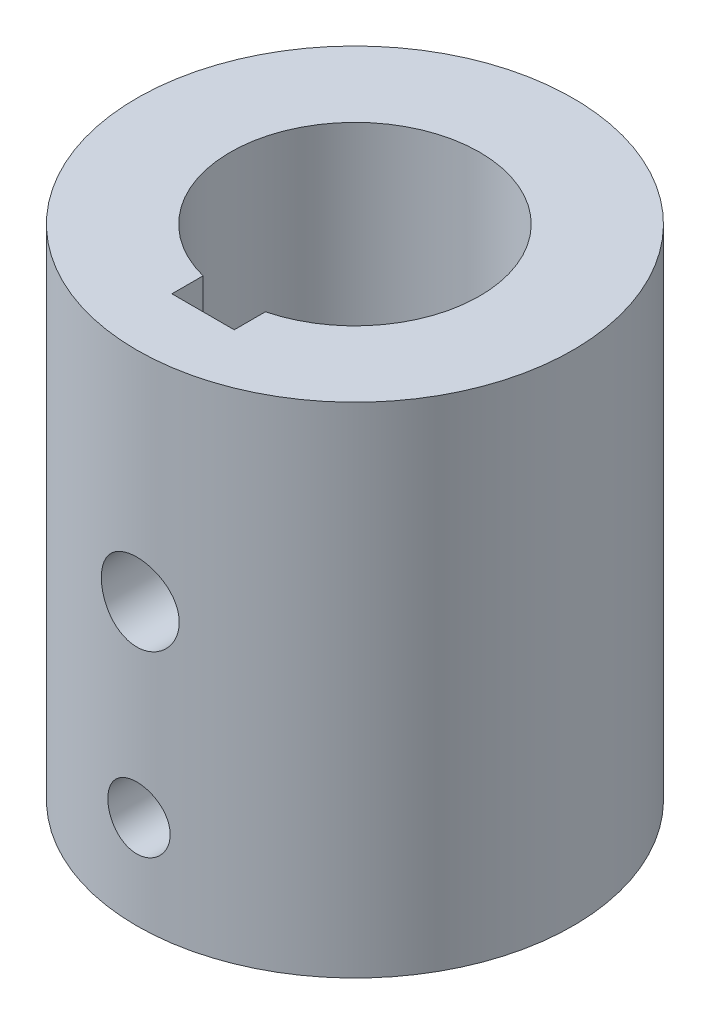
SolidWorks part; units mm, degrees
ref_plane "Front Plane" through (0, 0, 0) normal (0, 0, 1) x (1, 0, 0)
ref_plane "Top Plane" through (0, 0, 0) normal (0, 1, 0) x (1, 0, 0)
ref_plane "Right Plane" through (0, 0, 0) normal (1, 0, 0) x (0, 0, -1)
sketch "Sketch1" plane through (0, 0, 0) normal (0, 1, 0) x (1, 0, 0)
  circle A0 centre (0, 0) radius 12.7
  circle A1 centre (0, 0) radius 22.225
  dimension "D1" = 25.4
  dimension "D2" = 44.45
extrude "Boss-Extrude1" add sketch "Sketch1" along normal blind 50.8
sketch "Sketch2" plane through (0, 0, 0) normal (0, 0, 1) x (1, 0, 0)
  line L0 (-22.225, 0) -> (22.225, 0) construction
  line L1 (0, 0) -> (0, 9.525) construction
  circle A0 centre (0, 9.525) radius 3.175
  dimension "D1" = 6.35
  dimension "D2" = 9.525
extrude "Cut-Extrude1" cut sketch "Sketch2" against normal through all and the other way through all
hole_wizard "5/16 (0.3125) Diameter Hole1" positions "3DSketch2" profile "Sketch5" hole size "5/16" standard "Ansi Inch"
sketch3d "3DSketch2"
  line L0 (0, 0, 22.225) -> (0, 0, 0) construction
  line L1 (0, 0, 22.225) -> (0, 50.8, 22.225) construction
  circle A0 centre (0, 50.8, 0) radius 22.225 construction
  point P0 (0, 28.575, 22.225)
  point P13 (0, 73.025, 0)
  dimension "D1" = 22.225
sketch "Sketch5" plane through (0, 28.575, 22.225) normal (1, 0, 0) x (0, -1, 0)
  line L0 (0, 0) -> (0, 9.525)
  line L1 (0, 9.525) -> (3.9687, 9.525)
  line L2 (3.9687, 9.525) -> (3.9687, 0)
  line L5 (3.9687, 0) -> (0, 0)
  line L11 (0, -6.35) -> (0, 107.95) construction
  dimension "Thru Hole Dia." = 7.9375
  dimension "Thru Hole Depth" = 9.525
sketch "Sketch6" plane through (0, 50.8, 0) normal (0, 1, 0) x (1, 0, 0)
  line L0 (0, 0) -> (0, -15.4717) construction
  line L2 (3.175, -12.2967) -> (-3.175, -12.2967)
  line L3 (3.175, -12.2967) -> (3.175, -15.4717)
  line L4 (3.175, -15.4717) -> (-3.175, -15.4717)
  line L5 (-3.175, -12.2967) -> (-3.175, -15.4717)
  circle A0 centre (0, 0) radius 12.7 construction
  dimension "D1" = 6.35
  dimension "D2" = 3.175
extrude "Cut-Extrude3" cut sketch "Sketch6" against normal up to surface (50.8 mm away) up to face at (0, 0, 22.225)
